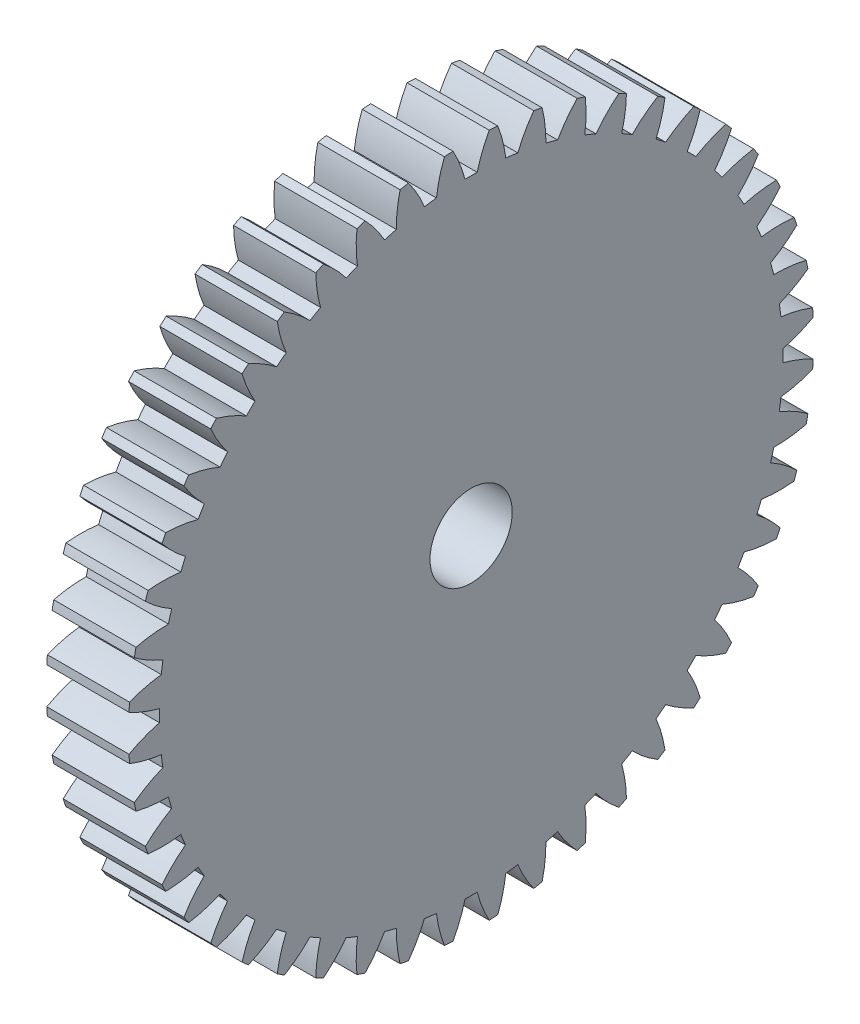
SolidWorks part; units mm, degrees
ref_plane "Plane1" through (0, 0, 0) normal (0, 0, 1) x (1, 0, 0)
ref_plane "Plane2" through (0, 0, 0) normal (0, 1, 0) x (1, 0, 0)
ref_plane "Plane3" through (0, 0, 0) normal (1, 0, 0) x (0, 0, -1)
sketch "HoldingSke" plane through (0, 0, 0) normal (0, 1, 0) x (1, 0, 0)
  line L0 (0, 0) -> (203.951, -226.5105)
  line L1 (-15, 0) -> (100, 0) construction
  line L2 (0, 0) -> (-2.1039, 2.3779)
  line L3 (0, 0) -> (-11.863, 4.5341)
  line L4 (0, 0) -> (5.7786, 6.4178)
  line L5 (0, 0) -> (-47.5972, -17.7524)
  line L6 (0, 0) -> (-10.5278, -7.1032)
  line L7 (-2.1039, 2.3779) -> (8.8308, 51.9871)
  line L8 (-76.2, 54.61) -> (-61.976, 54.61)
  line L9 (-71.009, 38.7566) -> (-53.1078, 45.2721)
  line L10 (-76.2, 71.12) -> (104.1128, 71.12)
  line L11 (0, 0) -> (-12.7, 0)
  line L12 (-76.2, 101.6) -> (-76.1147, 101.6)
  line L13 (24.9733, 27.94) -> (52.9518, 28.4284)
  line L14 (24.9733, 27.94) -> (24.9746, 27.94)
  line L15 (24.9733, 27.94) -> (100.4006, 29.5858)
  circle A0 centre (0, 0) radius 6.35
  circle A1 centre (0, 0) radius 38.1
  circle A2 centre (0, 0) radius 38.1
  circle A3 centre (0, 0) radius 6.35
  dimension "MHD" = 76.2
  dimension "Hub_dia" = 76.2
  dimension "Bore" = 12.7
  dimension "MBD" = 12.7
  dimension "Num_teeth" = 48
  dimension "Pitch" = 304.8
  dimension "Overall_len" = 50.8
  dimension "Show_teeth" = 48
  dimension "Thickness" = 12.7
  dimension "OAL" = 50.8001
  dimension "T_dim" = 14.224
  dimension "Ap" = 20
  dimension "H" = 19.05
  dimension "Pitch_radius" = 180.3128
  dimension "Width" = 12.7
  dimension "Backlash" = 0.0853
  dimension "Addendum_fac" = 1
  dimension "Dedendum_fac" = 1.25
  dimension "Clearance_fac" = 0.25
  dimension "Dedendum_add" = 0.0013
sketch "BasProSke" plane through (0, 0, 0) normal (0, 1, 0) x (1, 0, 0)
  line L0 (-10, 0) -> (60, 0) construction
  line L1 (0, 0) -> (0, 52.9167)
  line L2 (0, 0) -> (12.7, 0)
  line L3 (12.7, 0) -> (12.7, 52.9167)
  line L4 (12.7, 52.9167) -> (0, 52.9167)
  dimension "Thickness" = 12.7
  dimension "Diameter" = 105.8333
revolve "Base-Revolve" add sketch "BasProSke" angle 360 about L0
sketch "TooCutSke" plane through (0, 0, 0) normal (1, 0, 0) x (0, 0, -1)
  line L1 (0, 0) -> (0, 107) construction
  line L2 (0, 0) -> (-1.8115, 50.7677) construction
  line L3 (0, 0) -> (-6.642, 101.3375) construction
  line L4 (-1.8115, 50.7677) -> (-3.321, 50.6688) construction
  arc A0 (0.9387, 48.1437) -> (-0.9387, 48.1437) centre (0, 0) ccw
  arc A1 (2.8166, 52.8671) -> (-2.8166, 52.8671) centre (0, 0) ccw
  circle A2 centre (0, 0) radius 50.8 construction
  circle A3 centre (0, 0) radius 47.7364 construction
  arc A4 (-0.9387, 48.1437) -> (-2.8166, 52.8671) centre (-20.6117, 43.0572) ccw
  arc A5 (2.8166, 52.8671) -> (0.9387, 48.1437) centre (20.6117, 43.0572) ccw
  dimension "Root_dia" = 96.3058
  dimension "Overcut_dia" = 105.8841
  dimension "Pitch_dia" = 101.6
  dimension "Base_dia" = 95.4728
  dimension "Flank_rad" = 20.32
  dimension "Half_ang" = 3.75
  dimension "Half_CT" = 1.5128
extrude "ToothCut" cut sketch "TooCutSke" along normal through all
fillet "Breaks" [suppressed] radius 0.0423
fillet "RootFillets" [suppressed] radius 0.5304
pattern_circular "TeethCuts" count 48 every 7.5 about axis through (-10, 0, 0) along (1, 0, 0) of "ToothCut", "RootFillets", "Breaks"
sketch "HubNeaOneSke" plane through (0, 0, 0) normal (-1, 0, 0) x (0, 0, 1)
  circle A0 centre (0, 0) radius 38.1
  dimension "Diameter" = 76.2
extrude "HubNearOne" [suppressed] add sketch "HubNeaOneSke" along normal blind 38.1001
sketch "HubNeaBotSke" plane through (0, 0, 0) normal (-1, 0, 0) x (0, 0, 1)
  circle A0 centre (0, 0) radius 38.1
  dimension "Diameter" = 76.2
extrude "HubNearBoth" [suppressed] add sketch "HubNeaBotSke" along normal blind 19.05
ref_plane "FarPln" through (12.7, 0, 0) normal (1, 0, 0) x (0, 0, -1)
sketch "HubFarSke" plane through (12.7, 0, 0) normal (1, 0, 0) x (0, 0, -1)
  circle A0 centre (0, 0) radius 38.1
  dimension "Diameter" = 76.2
extrude "HubFar" [suppressed] add sketch "HubFarSke" along normal blind 19.05
sketch "BorSke" plane through (0, 0, 0) normal (1, 0, 0) x (0, 0, -1)
  circle A0 centre (0, 0) radius 6.35
  dimension "Diameter" = 12.7
extrude "Bore" cut sketch "BorSke" along normal mid plane 101.6001
sketch "KeySke" plane through (0, 0, 0) normal (1, 0, 0) x (0, 0, -1)
  line L0 (-1.5875, 0) -> (-1.5875, 7.874)
  line L1 (-1.5875, 7.874) -> (1.5875, 7.874)
  line L2 (1.5875, 7.874) -> (1.5875, 0)
  line L3 (0, 0) -> (0, 34) construction
  line L4 (-1.5875, 0) -> (1.5875, 0)
  dimension "Offset" = 7.874
  dimension "Width" = 3.175
extrude "Keyway" [suppressed] cut sketch "KeySke" along normal mid plane 101.6001
pattern_circular "Keyway2" [suppressed] count 2 every 90 about axis through (-10, 0, 0) along (1, 0, 0)
equation "' \"Pitch@HoldingSke\" = 4"
equation "' \"Num_teeth@HoldingSke\" = 12"
equation "' \"Ap@HoldingSke\" =  20"
equation "' \"Ap@HoldingSke\" = 20"
equation "' \"Width@HoldingSke\" = 0.5"
equation "' \"Hub_dia@HoldingSke\"= 1"
equation "' \"Hub_dia@HoldingSke\" = 1"
equation "' \"Overall_len@HoldingSke\" = 1.0"
equation "' \"Bore@HoldingSke\" = 0.75"
equation "' \"T_dim@HoldingSke\" = 0.85"
equation "' \"Width@KeySke\" = 0.25"
equation "' \"Show_teeth@HoldingSke\" = 13"
equation "' \"Backlash@HoldingSke\" = 0.009"
equation "' \"Addendum_fac@HoldingSke\" = 1.0"
equation "' \"Dedendum_fac@HoldingSke\" = 1.25"
equation "' \"Dedendum_add@HoldingSke\" = 0.00005"
equation "' \"Clearance_fac@HoldingSke\" = 0.25"
equation "' \"Pitch@HoldingSke\" = 0.5"
equation "' \"Num_teeth@HoldingSke\" = 23"
equation "' \"Show_teeth@HoldingSke\" = 23"
equation "' \"Backlash@HoldingSke\" = 0.0375"
equation "\"Overcut_dia@TooCutSke\" = (\"Num_teeth@HoldingSke\" + 2 * \"Addendum_fac@HoldingSke\") / \"Pitch@HoldingSke\" + 0.002"
equation "\"Pitch_dia@TooCutSke\" = \"Num_teeth@HoldingSke\" / \"Pitch@HoldingSke\""
equation "\"Base_dia@TooCutSke\" = \"Num_teeth@HoldingSke\" / \"Pitch@HoldingSke\" * cos((\"Ap@HoldingSke\"  * 3.14159265 / 180))"
equation "\"Root_dia@TooCutSke\" = (\"Num_teeth@HoldingSke\" + 2) / \"Pitch@HoldingSke\" - 2 * (\"Addendum_fac@HoldingSke\" + \"Dedendum_fac@HoldingSke\") / \"Pitch@HoldingSke\" - \"Dedendum_add@HoldingSke\" * 2"
equation "\"Half_ang@TooCutSke\" = 180 / \"Num_teeth@HoldingSke\""
equation "\"Half_CT@TooCutSke\" = \"Num_teeth@HoldingSke\" / \"Pitch@HoldingSke\" * sin((3.14159265 / 2 / \"Num_teeth@HoldingSke\")) / 2 - 7 * \"Backlash@HoldingSke\" / 4"
equation "\"Flank_rad@TooCutSke\" = \"Num_teeth@HoldingSke\" / \"Pitch@HoldingSke\" / 5"
equation "\"Radius@RootFillets\" = \"Clearance_fac@HoldingSke\" / \"Pitch@HoldingSke\" + \"Dedendum_add@HoldingSke\""
equation "\"Break_rad@Breaks\" = 0.02 / \"Pitch@HoldingSke\""
equation "\"Thickness@HoldingSke\" = \"Width@HoldingSke\""
equation "\"OAL@HoldingSke\" = \"Thickness@HoldingSke\""
equation "\"MHD@HoldingSke\" = (\"Num_teeth@HoldingSke\" + 2) / \"Pitch@HoldingSke\" - 2 * (\"Addendum_fac@HoldingSke\" + \"Dedendum_fac@HoldingSke\")  / \"Pitch@HoldingSke\" - \"Dedendum_add@HoldingSke\" * 2"
equation "\"MBD@HoldingSke\" = (\"Num_teeth@HoldingSke\" + 2) / \"Pitch@HoldingSke\" - 2 * (\"Addendum_fac@HoldingSke\" + \"Dedendum_fac@HoldingSke\")  / \"Pitch@HoldingSke\" - \"Dedendum_add@HoldingSke\" * 2 - 0.002"
equation "\"MHD@HoldingSke\" = ((sgn( \"MHD@HoldingSke\" - \"Hub_dia@HoldingSke\" )-1)*( \"MHD@HoldingSke\" - \"Hub_dia@HoldingSke\" ))/-2+ \"Hub_dia@HoldingSke\""
equation "\"MBD@HoldingSke\" = ((sgn( \"MBD@HoldingSke\" - \"Bore@HoldingSke\" )-1)*( \"MBD@HoldingSke\" - \"Bore@HoldingSke\" ))/-2+ \"Bore@HoldingSke\""
equation "\"OAL@HoldingSke\" = ((sgn( \"OAL@HoldingSke\" - \"Overall_len@HoldingSke\" )+1)*( \"OAL@HoldingSke\" - \"Overall_len@HoldingSke\" ))/2 + \"Overall_len@HoldingSke\" + 0.000002"
equation "\"Num_teeth@TeethCuts\" = int( \"Show_teeth@HoldingSke\" ) + 1"
equation "\"Num_teeth@TeethCuts\" = ((sgn( \"Num_teeth@TeethCuts\" - \"Num_teeth@HoldingSke\" )-1)*( \"Num_teeth@TeethCuts\" - \"Num_teeth@HoldingSke\" ))/-2+ \"Num_teeth@HoldingSke\""
equation "\"Num_teeth@TeethCuts\" = ((sgn( \"Num_teeth@TeethCuts\" - 2.0)+1)*( \"Num_teeth@TeethCuts\" - 2.0))/2 +2.0"
equation "\"Angle@TeethCuts\" = 360.0 / \"Num_teeth@HoldingSke\""
equation "\"Diameter@BasProSke\" = (\"Num_teeth@HoldingSke\" + 2 * \"Addendum_fac@HoldingSke\") / \"Pitch@HoldingSke\""
equation "\"Thickness@BasProSke\"  = \"Thickness@HoldingSke\""
equation "' \"Fillet_rad@BasProSke\" =  \"Thickness@HoldingSke\" * 0.05"
equation "' \"Fillet_rad@BasProSke\" = \"Thickness@HoldingSke\" * 0.05"
equation "\"MHD@HoldingSke\" = ((sgn( \"MHD@HoldingSke\" - \"Root_dia@TooCutSke\" )-1)*( \"MHD@HoldingSke\" - \"Root_dia@TooCutSke\" ))/-2+ \"Root_dia@TooCutSke\""
equation "\"Diameter@HubNeaOneSke\" = \"MHD@HoldingSke\""
equation "\"Length@HubNearOne\" = \"OAL@HoldingSke\" - \"Thickness@BasProSke\""
equation "\"Diameter@HubNeaBotSke\" = \"MHD@HoldingSke\""
equation "\"Length@HubNearBoth\" = ( \"OAL@HoldingSke\" - \"Thickness@BasProSke\" ) / 2.0"
equation "\"Thickness@FarPln\" = \"Thickness@BasProSke\""
equation "\"Diameter@HubFarSke\" = \"MHD@HoldingSke\""
equation "\"Length@HubFar\" = ( \"OAL@HoldingSke\" - \"Thickness@BasProSke\" ) / 2.0"
equation "\"Diameter@BorSke\" = \"MBD@HoldingSke\""
equation "\"D1@Bore\" = \"OAL@HoldingSke\" * 2.0"
equation "\"D1@Keyway\" = \"OAL@HoldingSke\" * 2.0"
equation "\"Offset@KeySke\" = \"T_dim@HoldingSke\" - \"MBD@HoldingSke\" / 2.0"
